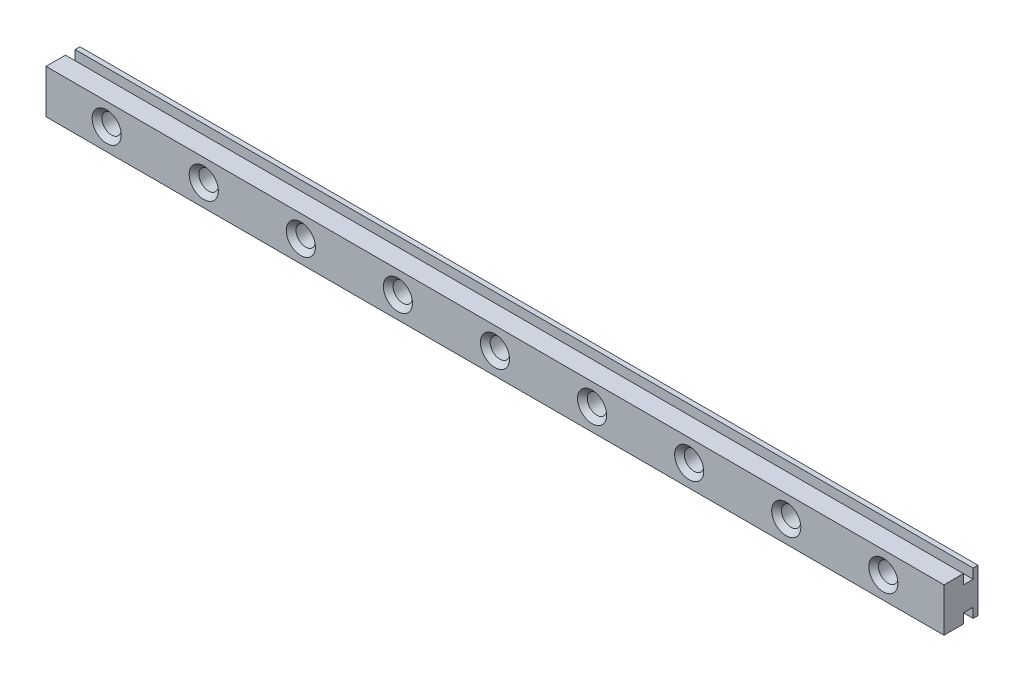
SolidWorks part; units mm, degrees
ref_plane "Plan de face" through (0, 0, 0) normal (0, 0, 1) x (1, 0, 0)
ref_plane "Plan de dessus" through (0, 0, 0) normal (0, 1, 0) x (1, 0, 0)
ref_plane "Plan de droite" through (0, 0, 0) normal (1, 0, 0) x (0, 0, -1)
sketch "Esquisse1" plane through (0, 0, 0) normal (0, 0, 1) x (1, 0, 0)
  line L0 (80, 0) -> (-80, 0) construction
  line L1 (92.5, -4.5) -> (-92.5, -4.5)
  line L2 (92.5, -4.5) -> (92.5, 4.5)
  line L3 (92.5, 4.5) -> (-92.5, 4.5)
  line L4 (-92.5, -4.5) -> (-92.5, 4.5)
  line L5 (92.5, -4.5) -> (-92.5, 4.5) construction
  line L6 (92.5, 4.5) -> (-92.5, -4.5) construction
  circle A0 centre (-80, 0) radius 2
  circle A1 centre (-60, 0) radius 2
  circle A2 centre (-40, 0) radius 2
  circle A3 centre (-20, 0) radius 2
  circle A4 centre (0, 0) radius 2
  circle A5 centre (20, 0) radius 2
  circle A6 centre (40, 0) radius 2
  circle A7 centre (60, 0) radius 2
  circle A8 centre (80, 0) radius 2
  point P0 (0, 0)
  point P9 (0, 0)
  dimension "D3" = 4
  dimension "D1" = 185
  dimension "D2" = 160
  dimension "D4" = 9
  dimension "D5" = 9
extrude "Boss.-Extru.1" add sketch "Esquisse1" along normal blind 7
sketch "Esquisse2" plane through (-92.5, 0, 0) normal (-1, 0, 0) x (0, 0, 1)
  line L0 (7, 4.5) -> (0, 4.5) construction
  line L1 (3, 2.5) -> (1, 2.5)
  line L2 (3, 2.5) -> (3, 4.5)
  line L3 (3, 4.5) -> (1, 4.5)
  line L4 (1, 2.5) -> (1, 4.5)
  line L5 (3, 2.5) -> (1, 4.5) construction
  line L6 (3, 4.5) -> (1, 2.5) construction
  line L7 (0, 4.5) -> (0, -4.5) construction
  line L8 (0, 0) -> (7, 0) construction
  line L9 (7, 4.5) -> (7, -4.5) construction
  line L10 (1, -2.5) -> (1, -4.5)
  line L11 (3, -4.5) -> (1, -4.5)
  line L12 (3, -2.5) -> (3, -4.5)
  line L13 (3, -2.5) -> (1, -2.5)
  point P0 (2, 3.5)
  dimension "D1" = 2
  dimension "D2" = 1
extrude "Enlèv. mat.-Extru.1" cut sketch "Esquisse2" against normal up to next
chamfer "Chanfrein1" distance 1 angle 45 9 edges at (82, 0, 7) (62, 0, 7) (42, 0, 7) (22, 0, 7) (2, 0, 7) (-18, 0, 7) (-38, 0, 7) (-58, 0, 7) (-78, 0, 7)
